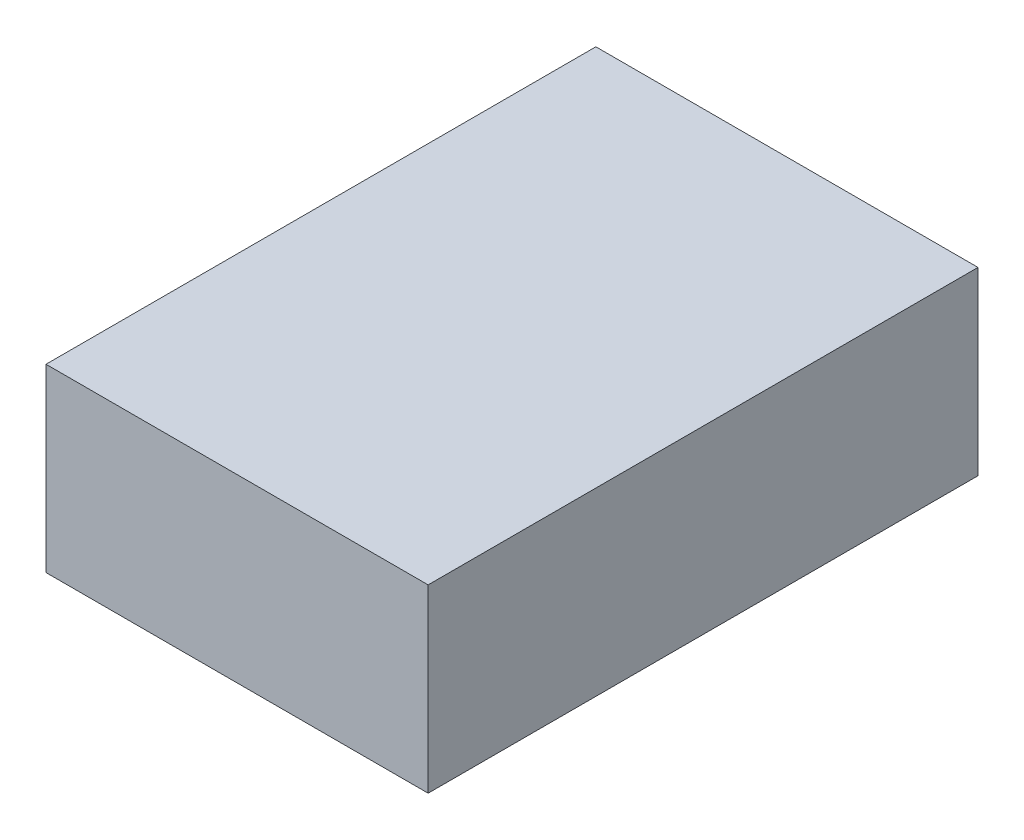
SolidWorks part; units mm, degrees
ref_plane "Front Plane" through (0, 0, 0) normal (0, 0, 1) x (1, 0, 0)
ref_plane "Top Plane" through (0, 0, 0) normal (0, 1, 0) x (1, 0, 0)
ref_plane "Right Plane" through (0, 0, 0) normal (1, 0, 0) x (0, 0, -1)
sketch "Sketch1" plane through (0, 0, 0) normal (0, 0, 1) x (1, 0, 0)
  line L1 (-35.7347, 199.4188) -> (65.4879, 199.4188)
  line L2 (-35.7347, 199.4188) -> (-35.7347, 151.624)
  line L3 (-35.7347, 151.624) -> (65.4879, 151.624)
  line L4 (65.4879, 199.4188) -> (65.4879, 151.624)
extrude "Boss-Extrude1" add sketch "Sketch1" along normal blind 140.6497 and the other way blind 5
